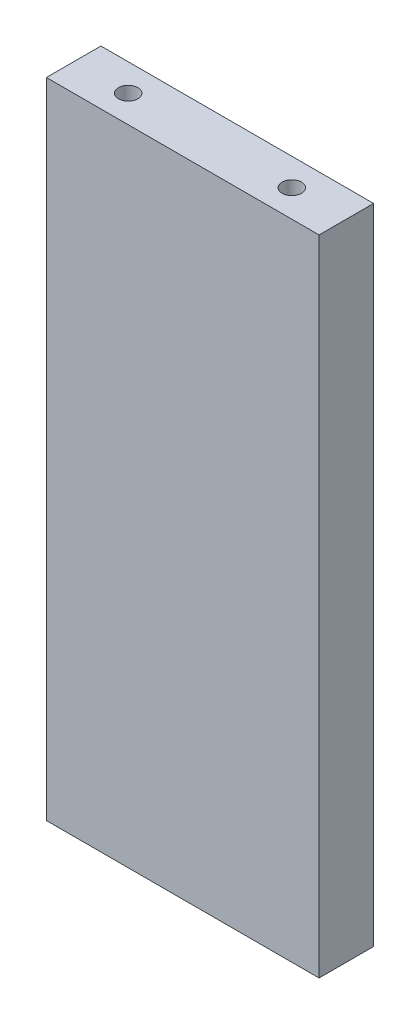
SolidWorks part; units mm, degrees
ref_plane "Front Plane" through (0, 0, 0) normal (0, 0, 1) x (1, 0, 0)
ref_plane "Top Plane" through (0, 0, 0) normal (0, 1, 0) x (1, 0, 0)
ref_plane "Right Plane" through (0, 0, 0) normal (1, 0, 0) x (0, 0, -1)
sketch "Sketch1" plane through (0, 0, 0) normal (0, 1, 0) x (1, 0, 0)
  line L1 (15.875, 3.175) -> (-15.875, 3.175)
  line L2 (15.875, 3.175) -> (15.875, -3.175)
  line L3 (15.875, -3.175) -> (-15.875, -3.175)
  line L4 (-15.875, 3.175) -> (-15.875, -3.175)
  line L5 (15.875, 3.175) -> (-15.875, -3.175) construction
  line L6 (15.875, -3.175) -> (-15.875, 3.175) construction
  point P0 (0, 0)
  dimension "D1" = 6.35
  dimension "D2" = 31.75
extrude "Boss-Extrude1" add sketch "Sketch1" along normal blind 74.93
hole_wizard "#4-40 Tapped Hole1" positions "Sketch2" profile "Sketch3" tap size "#4-40" standard "ANSI Inch"
sketch "Sketch2" plane through (0, 0, 0) normal (0, -1, 0) x (-1, 0, 0)
  line L0 (15.875, 3.175) -> (15.875, -3.175) construction
  line L1 (-15.875, -3.175) -> (-15.875, 3.175) construction
  point P0 (9.525, 0)
  point P2 (-9.525, 0)
  dimension "D1" = 6.35
  dimension "D2" = 6.35
sketch "Sketch3" plane through (-9.525, 0, 0) normal (1, 0, 0) x (0, 0, -1)
  line L0 (0, 0) -> (0, 8.2738)
  line L1 (0, 8.2738) -> (1.1303, 7.5946)
  line L2 (1.1303, 7.5946) -> (1.1303, 0)
  line L5 (1.1303, 0) -> (0, 0)
  line L10 (0, 8.2738) -> (-1.1303, 7.5946) construction
  line L11 (0, -6.35) -> (0, 107.95) construction
  dimension "Tap Drill Dia." = 2.2606
  dimension "Tap Drill Depth" = 7.5946
  dimension "Drill Angle" = 118
cosmetic thread "Hole Thread1"
cosmetic thread "Hole Thread2"
hole_wizard "#4-40 Tapped Hole2" positions "Sketch4" profile "Sketch5" tap size "#4-40" standard "ANSI Inch"
sketch "Sketch4" plane through (0, 74.93, 0) normal (0, 1, 0) x (1, 0, 0)
  line L0 (-15.875, 3.175) -> (-15.875, -3.175) construction
  line L1 (15.875, -3.175) -> (15.875, 3.175) construction
  point P0 (-9.525, 0)
  point P2 (9.525, 0)
  dimension "D1" = 6.35
  dimension "D2" = 6.35
sketch "Sketch5" plane through (-9.525, 74.93, 0) normal (1, 0, 0) x (0, 0, 1)
  line L0 (0, 0) -> (0, 8.2738)
  line L1 (0, 8.2738) -> (1.1303, 7.5946)
  line L2 (1.1303, 7.5946) -> (1.1303, 0)
  line L5 (1.1303, 0) -> (0, 0)
  line L10 (0, 8.2738) -> (-1.1303, 7.5946) construction
  line L11 (0, -6.35) -> (0, 107.95) construction
  dimension "Tap Drill Dia." = 2.2606
  dimension "Tap Drill Depth" = 7.5946
  dimension "Drill Angle" = 118
cosmetic thread "Hole Thread3"
cosmetic thread "Hole Thread4"
